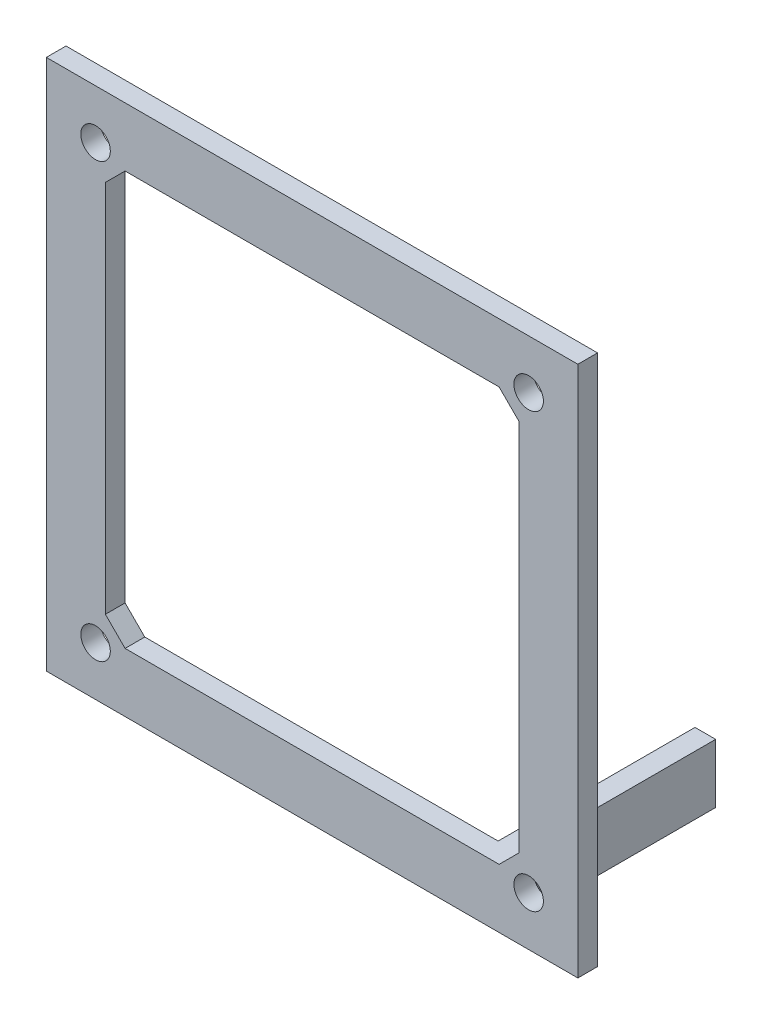
SolidWorks part; units mm, degrees
ref_plane "Alzado" through (0, 0, 0) normal (0, 0, 1) x (1, 0, 0)
ref_plane "Planta" through (0, 0, 0) normal (0, 1, 0) x (1, 0, 0)
ref_plane "Vista lateral" through (0, 0, 0) normal (1, 0, 0) x (0, 0, -1)
sketch "Croquis1" plane through (0, 0, 0) normal (0, 0, 1) x (1, 0, 0)
  line L0 (-73.7748, 23.7674) -> (-23.7748, -26.2326) construction
  line L1 (-73.7748, 23.7674) -> (-23.7748, 23.7674)
  line L2 (-73.7748, 23.7674) -> (-73.7748, -26.2326)
  line L3 (-73.7748, -26.2326) -> (-23.7748, -26.2326)
  line L4 (-23.7748, 23.7674) -> (-23.7748, -26.2326)
  line L5 (-73.7748, -26.2326) -> (-23.7748, 23.7674) construction
  line L9 (-69.7748, 17.7674) -> (-67.7748, 19.7674)
  line L12 (-29.7748, 19.7674) -> (-27.7748, 17.7674)
  line L14 (-27.7748, -20.2326) -> (-29.7748, -22.2326)
  line L16 (-67.7748, -22.2326) -> (-69.7748, -20.2326)
  line L17 (-69.7748, -20.2326) -> (-69.7748, 17.7674)
  line L18 (-67.7748, 19.7674) -> (-29.7748, 19.7674)
  line L19 (-27.7748, 17.7674) -> (-27.7748, -20.2326)
  line L20 (-29.7748, -22.2326) -> (-67.7748, -22.2326)
  circle A0 centre (-70.7748, 20.7674) radius 1.5
  circle A1 centre (-26.7748, 20.7674) radius 1.5
  circle A2 centre (-26.7748, -23.2326) radius 1.5
  circle A3 centre (-70.7748, -23.2326) radius 1.5
  dimension "D3" = 3
  dimension "D1" = 50
  dimension "D2" = 50
  dimension "D4" = 3
  dimension "D5" = 2
  dimension "D6" = 2
extrude "Saliente-Extruir1" add sketch "Croquis1" along normal blind 2
sketch "Croquis2" plane through (0, 0, 0) normal (0, 0, -1) x (-1, 0, 0)
  line L0 (23.7748, -26.2326) -> (23.7748, 23.7674) construction
  line L1 (21.7748, 25.7674) -> (75.7748, 25.7674)
  line L2 (21.7748, 25.7674) -> (21.7748, -28.2326)
  line L3 (21.7748, -28.2326) -> (75.7748, -28.2326)
  line L4 (75.7748, 25.7674) -> (75.7748, -28.2326)
  line L5 (73.7748, 23.7674) -> (73.7748, -26.2326) construction
  line L6 (23.7748, 23.7674) -> (73.7748, 23.7674) construction
  line L7 (73.7748, -26.2326) -> (23.7748, -26.2326) construction
  line L9 (23.7748, 23.7674) -> (73.7748, 23.7674)
  line L10 (23.7748, 23.7674) -> (23.7748, -26.2326)
  line L11 (23.7748, -26.2326) -> (73.7748, -26.2326)
  line L12 (73.7748, 23.7674) -> (73.7748, -26.2326)
  dimension "D1" = 2
  dimension "D2" = 2
  dimension "D3" = 2
  dimension "D4" = 2
extrude "Saliente-Extruir2" add sketch "Croquis2" against normal blind 2
sketch "Croquis3" plane through (0, 0, 0) normal (0, 0, -1) x (-1, 0, 0)
  line L0 (21.7748, 25.7674) -> (21.7748, -28.2326) construction
  line L1 (29.7748, -22.2326) -> (31.8748, -22.2326)
  line L2 (29.7748, -22.2326) -> (29.7748, -28.2326)
  line L3 (29.7748, -28.2326) -> (31.8748, -28.2326)
  line L4 (31.8748, -22.2326) -> (31.8748, -28.2326)
  line L5 (21.7748, -28.2326) -> (75.7748, -28.2326) construction
  dimension "D1" = 8
  dimension "D2" = 6
  dimension "D3" = 0
  dimension "D4" = 2.1
extrude "Saliente-Extruir3" add sketch "Croquis3" along normal blind 20
